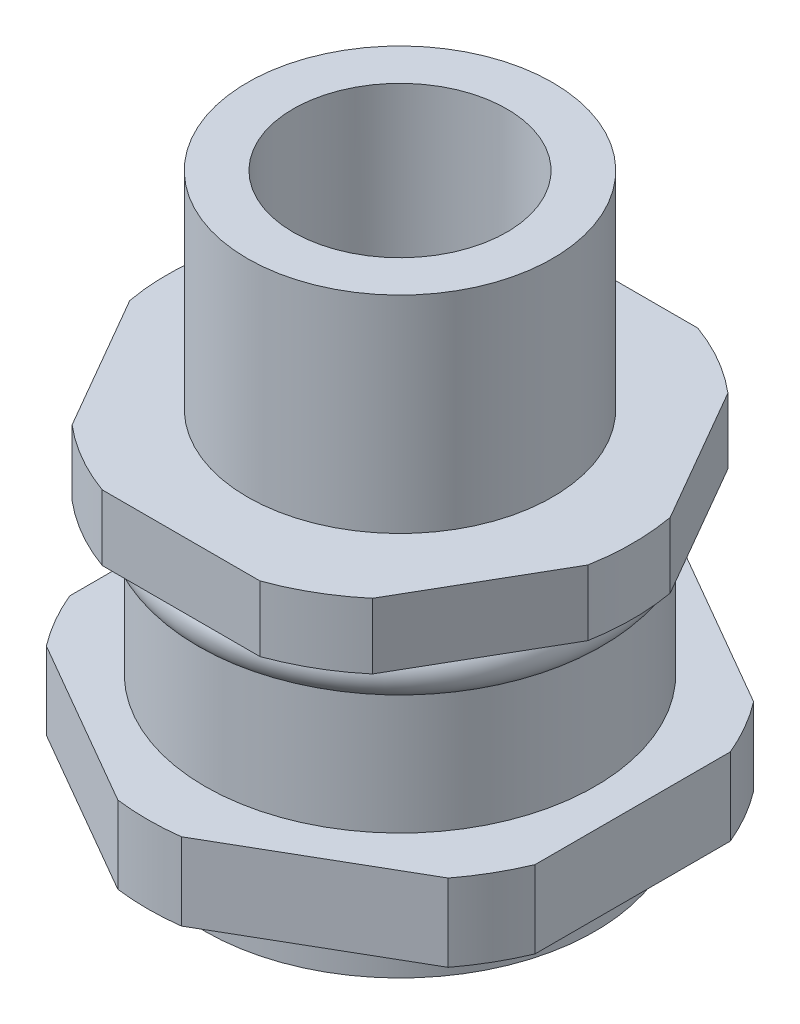
SolidWorks part; units mm, degrees
ref_plane "Front Plane" through (0, 0, 0) normal (0, 0, 1) x (1, 0, 0)
ref_plane "Top Plane" through (0, 0, 0) normal (0, 1, 0) x (1, 0, 0)
ref_plane "Right Plane" through (0, 0, 0) normal (1, 0, 0) x (0, 0, -1)
sketch "Sketch2" plane through (0, 0, 0) normal (0, 1, 0) x (1, 0, 0)
  circle A0 centre (0, 0) radius 5.9118
  dimension "D1" = 11.8237
extrude "Boss-Extrude1" add sketch "Sketch2" along normal blind 8.001
sketch "Sketch3" plane through (0, 0, 0) normal (0, -1, 0) x (1, 0, 0)
  circle A0 centre (0, 0) radius 9.017
  dimension "D1" = 18.034
extrude "Boss-Extrude2" add sketch "Sketch3" along normal blind 2.54
sketch "Sketch4" plane through (0, 0, 0) normal (0, 1, 0) x (1, 0, 0)
  line L1 (4.898, 8.4836) -> (-4.898, 8.4836)
  line L2 (-4.898, 8.4836) -> (-9.796, 0)
  line L3 (-9.796, 0) -> (-4.898, -8.4836)
  line L4 (-4.898, -8.4836) -> (4.898, -8.4836)
  line L5 (4.898, -8.4836) -> (9.796, 0)
  line L6 (9.796, 0) -> (4.898, 8.4836)
  circle A0 centre (0, 0) radius 8.4836 construction
  circle A1 centre (0, 0) radius 9.017 construction
  circle A2 centre (0, 0) radius 9.017
  circle M8 centre (0, 0) radius 9.017
  dimension "D1" = 16.9672
extrude "Cut-Extrude1" cut sketch "Sketch4" against normal blind 2.54 contours L3 M8 | L2 M8 | L6 M8 | L4 M8 | L5 M8 | L1 M8 | A2
sketch "Sketch5" plane through (0, -2.54, 0) normal (0, -1, 0) x (1, 0, 0)
  circle A0 centre (0, 0) radius 7.5565
  dimension "D1" = 15.113
extrude "Boss-Extrude3" add sketch "Sketch5" along normal blind 11.2141
sketch "Sketch6" plane through (0, 0, 0) normal (0, 0, 1) x (1, 0, 0)
  line L0 (-7.5565, -2.54) -> (7.5565, -2.54) construction
  line L2 (0, 0) -> (0, -13.7541) construction
  line L3 (-7.5565, -13.7541) -> (7.5565, -13.7541) construction
  circle A0 centre (7.1882, -3.429) radius 0.889
  point P5 (8.0772, -3.429)
  dimension "D1" = 1.778
  dimension "D2" = 8.0772
revolve "Revolve1" add sketch "Sketch6" angle 360 about L2
sketch "Sketch7" plane through (0, -2.54, 0) normal (0, -1, 0) x (1, 0, 0)
  line L1 (9.017, -3.7845) -> (9.017, 3.7845)
  line L2 (7.786, 5.9167) -> (1.231, 9.7012)
  line L3 (-1.231, 9.7012) -> (-7.786, 5.9167)
  line L4 (-9.017, 3.7845) -> (-9.017, -3.7845)
  line L5 (-7.786, -5.9167) -> (-1.231, -9.7012)
  line L6 (1.231, -9.7012) -> (7.786, -5.9167)
  circle A0 centre (0, 0) radius 9.017 construction
  arc A1 (-9.017, -3.7845) -> (-7.786, -5.9167) centre (0, 0) ccw
  arc A2 (-1.231, -9.7012) -> (1.231, -9.7012) centre (0, 0) ccw
  arc A3 (-7.786, 5.9167) -> (-9.017, 3.7845) centre (0, 0) ccw
  arc A4 (1.231, 9.7012) -> (-1.231, 9.7012) centre (0, 0) ccw
  arc A5 (9.017, 3.7845) -> (7.786, 5.9167) centre (0, 0) ccw
  arc A6 (7.786, -5.9167) -> (9.017, -3.7845) centre (0, 0) ccw
  dimension "D2" = 19.558
  dimension "D1" = 18.034
extrude "Boss-Extrude4" add sketch "Sketch7" along normal blind 2.9972 from offset 6.35
sketch "Sketch8" plane through (0, 8.001, 0) normal (0, 1, 0) x (1, 0, 0)
  circle A0 centre (0, 0) radius 4.1402
  dimension "D1" = 8.2804
extrude "Cut-Extrude2" cut sketch "Sketch8" against normal up to surface (8.001 mm away) up to face at (0, 0, 5.9118)
